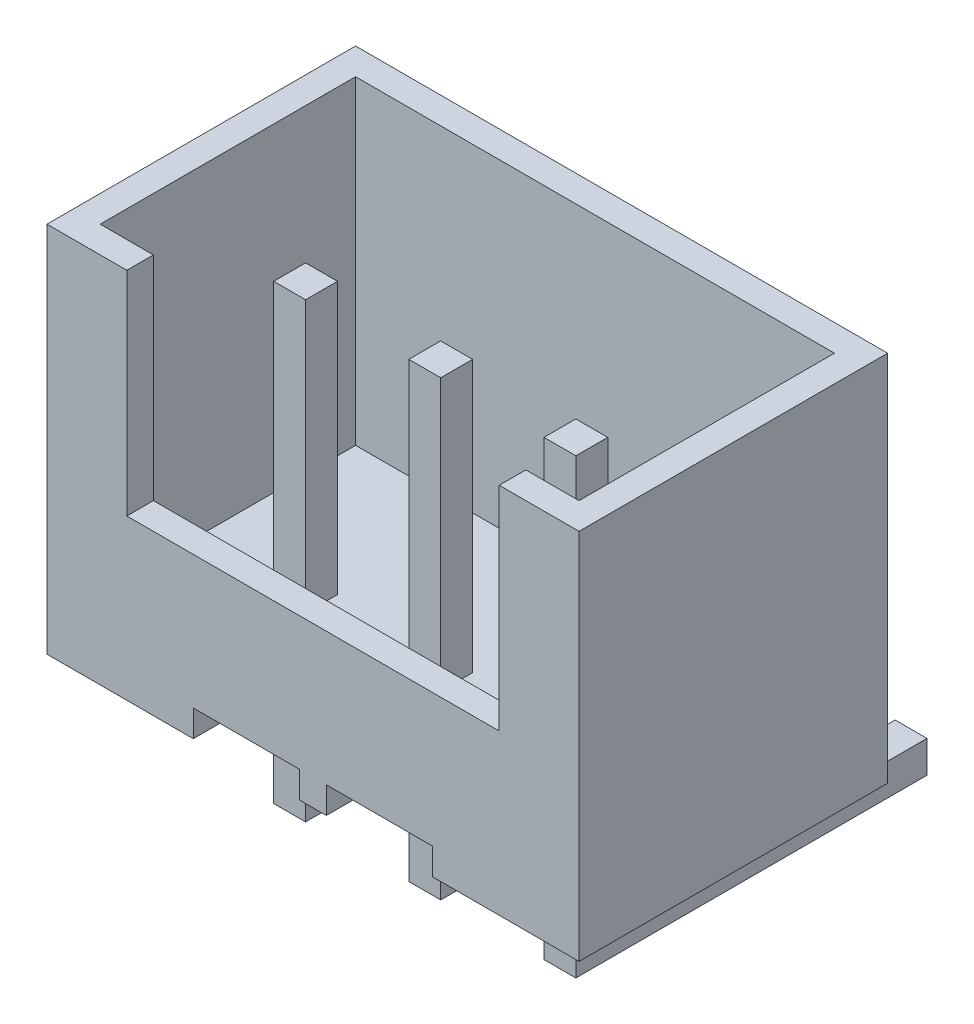
SolidWorks part; units mm, degrees
ref_plane "前视基准面" through (0, 0, 0) normal (0, 0, 1) x (1, 0, 0)
ref_plane "上视基准面" through (0, 0, 0) normal (0, 1, 0) x (1, 0, 0)
ref_plane "右视基准面" through (0, 0, 0) normal (1, 0, 0) x (0, 0, -1)
sketch "草图1" plane through (0, 0, 0) normal (0, 0, 1) x (1, 0, 0)
  line L0 (2.75, 0) -> (2.75, 0.5)
  line L1 (0, 0) -> (2.75, 0)
  line L2 (0, 0) -> (0, 7)
  line L3 (0, 7) -> (10, 7)
  line L4 (10, 0) -> (10, 7)
  line L5 (2.75, 0.5) -> (4.75, 0.5)
  line L6 (4.75, 0.5) -> (4.75, 0)
  line L7 (5.25, 0) -> (5.25, 0.5)
  line L8 (5.25, 0.5) -> (7.25, 0.5)
  line L9 (7.25, 0.5) -> (7.25, 0)
  line L10 (4.75, 0) -> (5.25, 0)
  line L11 (7.25, 0) -> (10, 0)
  line L12 (5, 4.6706) -> (5, 50004.6706) construction
  dimension "D1" = 10
  dimension "D2" = 7
  dimension "D3" = 2.5
  dimension "D4" = 0.5
  dimension "D5" = 0.5
extrude "凸台-拉伸1" add sketch "草图1" along normal blind 5.8
sketch "草图2" plane through (0, 7, 0) normal (0, 1, 0) x (1, 0, 0)
  line L0 (0, -5.8) -> (0, 0) construction
  line L1 (0.5, -0.5) -> (9.5, -0.5)
  line L2 (0.5, -0.5) -> (0.5, -5.3)
  line L3 (0.5, -5.3) -> (9.5, -5.3)
  line L4 (9.5, -0.5) -> (9.5, -5.3)
  line L5 (10, 0) -> (0, 0) construction
  line L6 (10, -5.8) -> (10, 0) construction
  line L7 (10, -5.8) -> (0, -5.8) construction
  dimension "D1" = 0.5
  dimension "D2" = 0.5
  dimension "D3" = 0.5
  dimension "D4" = 0.5
extrude "切除-拉伸1" cut sketch "草图2" against normal blind 6
sketch "草图3" plane through (0, 0, 0) normal (0, -1, 0) x (1, 0, 0)
  line L0 (2.75, 0) -> (4.75, 0) construction
  line L1 (2.16, 3.7) -> (2.76, 3.7)
  line L2 (2.16, 3.7) -> (2.16, 3.1)
  line L3 (2.16, 3.1) -> (2.76, 3.1)
  line L4 (2.76, 3.7) -> (2.76, 3.1)
  line L5 (5, 3.7) -> (5, 3.1) construction
  line L6 (2.46, 3.7) -> (2.46, 3.1) construction
  line L7 (0, 5.8) -> (0, 0) construction
  line L8 (5, 2.7254) -> (5, 50002.7254) construction
  line L11 (4.7, 3.7) -> (4.7, 3.1)
  line L12 (5.3, 3.1) -> (4.7, 3.1)
  line L13 (5.3, 3.7) -> (5.3, 3.1)
  line L14 (5.3, 3.7) -> (4.7, 3.7)
  line L15 (7.24, 3.7) -> (7.24, 3.1)
  line L16 (7.24, 3.1) -> (7.84, 3.1)
  line L17 (7.84, 3.1) -> (7.84, 3.7)
  line L18 (7.84, 3.7) -> (7.24, 3.7)
  line L19 (7.54, 3.7) -> (7.54, 3.1) construction
  dimension "D1" = 0.6
  dimension "D2" = 3.1
  dimension "D3" = 2.54
  dimension "D4" = 0.6
  dimension "D5" = 2.54
  dimension "D6" = 5
  dimension "D7" = 2.54
extrude "凸台-拉伸2" add sketch "草图3" against normal blind 6.1 and the other way blind 2.4
sketch "草图5" plane through (0, 0, 5.8) normal (0, 0, 1) x (1, 0, 0)
  line L0 (0, 7) -> (0, 0) construction
  line L2 (1.5, 7) -> (1.5, 3)
  line L3 (10, 7) -> (0, 7) construction
  line L4 (1.5, 3) -> (8.5, 3)
  line L5 (8.5, 3) -> (8.5, 7)
  line L6 (1.5, 7) -> (8.5, 7)
  line L7 (10, 0) -> (10, 7) construction
  dimension "D1" = 1.5
  dimension "D2" = 1.5
  dimension "D3" = 4
extrude "切除-拉伸2" cut sketch "草图5" against normal blind 1
sketch "草图6" plane through (0, 0, 3.1) normal (0, 0, -1) x (-1, 0, 0)
  line L0 (-2.16, -2.4) -> (-2.16, 0) construction
  line L1 (-2.76, -2.4) -> (-2.16, -2.4)
  line L2 (-2.76, -2.4) -> (-2.76, -1.8)
  line L3 (-2.76, -1.8) -> (-2.16, -1.8)
  line L4 (-2.16, -2.4) -> (-2.16, -1.8)
  line L5 (-4.7, -2.4) -> (-4.7, 0.5) construction
  line L6 (-5.3, -2.4) -> (-4.7, -2.4)
  line L7 (-5.3, -2.4) -> (-5.3, -1.8)
  line L8 (-5.3, -1.8) -> (-4.7, -1.8)
  line L9 (-4.7, -2.4) -> (-4.7, -1.8)
  line L10 (-7.24, -2.4) -> (-7.24, 0.5) construction
  line L11 (-7.84, -2.4) -> (-7.24, -2.4)
  line L12 (-7.84, -2.4) -> (-7.84, -1.8)
  line L13 (-7.84, -1.8) -> (-7.24, -1.8)
  line L14 (-7.24, -2.4) -> (-7.24, -1.8)
  dimension "D1" = 0.6
extrude "凸台-拉伸3" add sketch "草图6" along normal blind 6
